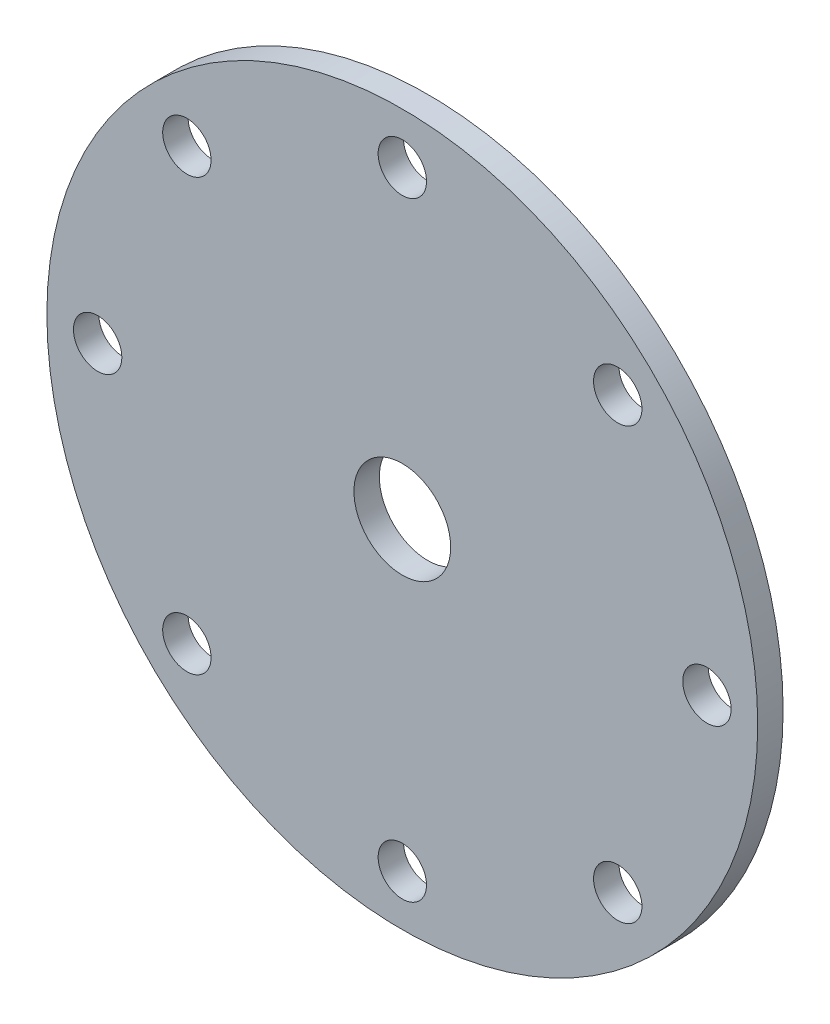
SolidWorks part; units mm, degrees
material "Plain Carbon Steel"
ref_plane "Front Plane" through (0, 0, 0) normal (0, 0, 1) x (1, 0, 0)
ref_plane "Top Plane" through (0, 0, 0) normal (0, 1, 0) x (1, 0, 0)
ref_plane "Right Plane" through (0, 0, 0) normal (1, 0, 0) x (0, 0, -1)
sketch "Sketch1" plane through (0, 0, 0) normal (0, 0, 1) x (1, 0, 0)
  line L0 (0, 70) -> (0, -70) construction
  line L1 (-70, 0) -> (70, 0) construction
  line L2 (-42.4264, 42.4264) -> (42.4264, -42.4264) construction
  line L3 (-42.4264, -42.4264) -> (42.4264, 42.4264) construction
  circle A0 centre (0, 0) radius 70
  circle A1 centre (0, 0) radius 9.525
  circle A2 centre (0, 60) radius 4.7625
  circle A6 centre (42.4264, 42.4264) radius 4.7625
  circle A7 centre (60, 0) radius 4.7625
  circle A8 centre (42.4264, -42.4264) radius 4.7625
  circle A9 centre (0, -60) radius 4.7625
  circle A10 centre (-42.4264, -42.4264) radius 4.7625
  circle A11 centre (-60, 0) radius 4.7625
  circle A12 centre (-42.4264, 42.4264) radius 4.7625
  dimension "D1" = 140
  dimension "D2" = 19.05
  dimension "D3" = 9.525
  dimension "D6" = 10
  dimension "D4" = 10
  dimension "D5" = 8
extrude "Rotor Disc" add sketch "Sketch1" along normal blind 5
